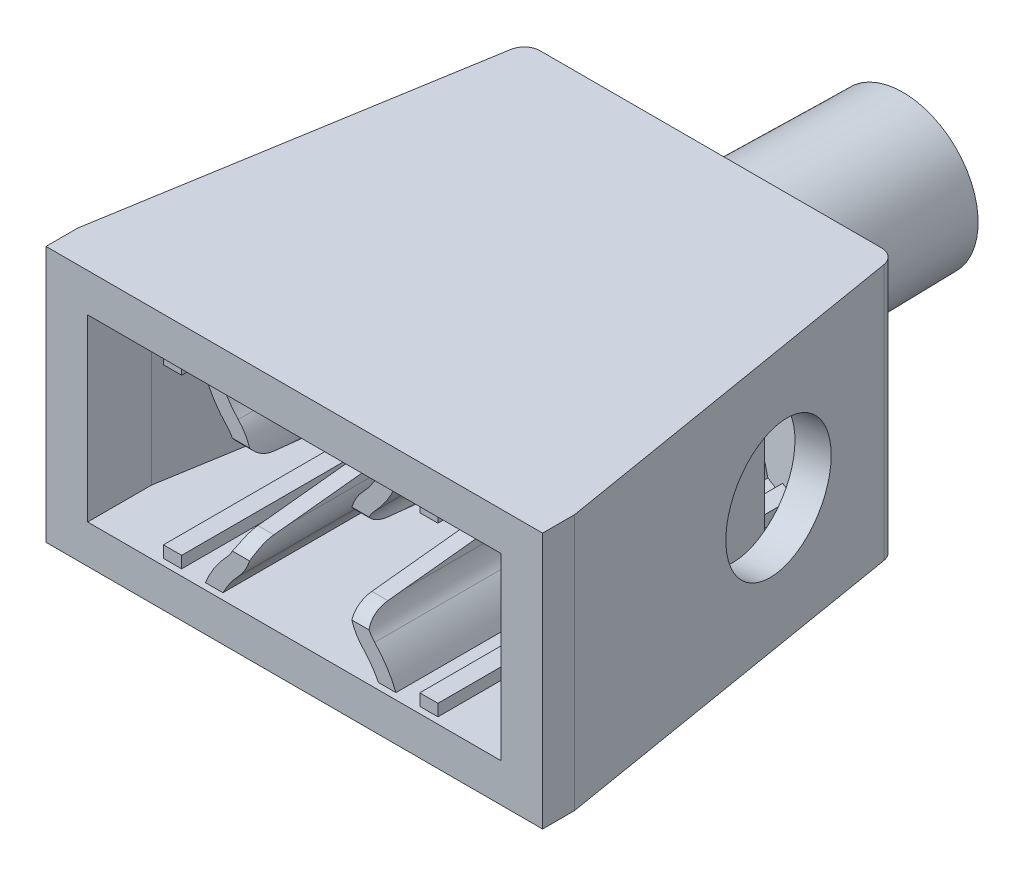
SolidWorks part; units mm, degrees
ref_plane "Front Plane" through (0, 0, 0) normal (0, 0, 1) x (1, 0, 0)
ref_plane "Top Plane" through (0, 0, 0) normal (0, 1, 0) x (1, 0, 0)
ref_plane "Right Plane" through (0, 0, 0) normal (1, 0, 0) x (0, 0, -1)
sketch "Sketch3" plane through (0, 0, 0) normal (0, 1, 0) x (1, 0, 0)
  line L0 (7.75, 0) -> (-7.75, 0)
  line L1 (-55, 0) -> (55, 0) construction
  line L2 (-7.75, 0) -> (-7.75, 1)
  line L3 (-7.75, 1) -> (-5.75, 13)
  line L4 (-5.75, 13) -> (5.75, 13)
  line L5 (0, -55) -> (0, 55) construction
  line L6 (0, 13) -> (0, 0)
  line L7 (7.75, 1) -> (5.75, 13)
  line L8 (7.75, 0) -> (7.75, 1)
  dimension "D1" = 7.75
  dimension "D2" = 1
  dimension "D3" = 5.75
  dimension "D4" = 13
extrude "Boss-Extrude1" add sketch "Sketch3" along normal blind 8 contours L4 L7 L8 L0 L2 L3
fillet "Fillet1" radius 0.5 2 edges at (5.75, 4, -13) (-5.75, 4, -13)
sketch "Sketch5" plane through (0, 0, -13) normal (0, 0, -1) x (-1, 0, 0)
  line L0 (0, 55) -> (0, -55) construction
  circle A0 centre (0, 4.196) radius 2.45
  dimension "D1" = 4.9
extrude "Boss-Extrude2" add sketch "Sketch5" along normal blind 6 draft 1
sketch "Sketch7" plane through (7.7027, 0, -1.2838) normal (0.9864, 0, -0.1644) x (-0.1644, 0, -0.9864)
  line L0 (11.4543, 0) -> (11.4543, 8) construction
  line L1 (-0.2877, 8) -> (11.4543, 8) construction
  circle A0 centre (7.4543, 4) radius 2
  dimension "D1" = 4
  dimension "D2" = 4
sketch "Sketch8" plane through (-7.7027, 0, -1.2838) normal (-0.9864, 0, -0.1644) x (-0.1644, 0, 0.9864)
  line L0 (-11.4543, 8) -> (-11.4543, 0) construction
  line L1 (0.2877, 8) -> (-11.4543, 8) construction
  circle A0 centre (-7.4543, 4) radius 2
  dimension "D1" = 4
  dimension "D2" = 4
ref_plane "Plane4" through (0, 4, 0) normal (0, 1, 0) x (1, 0, 0)
sketch "Sketch9" plane through (0, 4, 0) normal (0, 1, 0) x (1, 0, 0)
  line L0 (-6.45, 0) -> (-6.45, 2)
  line L2 (-4.4, 0) -> (4.4, 0) construction
  line L3 (-6.45, 2) -> (-4.95, 11)
  line L4 (-4.95, 11) -> (-2.4675, 12)
  line L5 (-2.4675, 12) -> (-1.4806, 12)
  line L6 (-1.4806, 12) -> (1.4806, 12)
  line L10 (6.45, 0) -> (-6.45, 0)
  line L12 (-7.75, 0) -> (-7.75, 1) construction
  line L15 (-5.3264, 13) -> (5.3264, 13) construction
  line L16 (-2.3453, 19) -> (-2.45, 13) construction
  line L17 (-7.75, 1) -> (-5.8196, 12.5822) construction
  line L19 (2.4675, 12) -> (1.4806, 12)
  line L20 (5.0967, 11) -> (2.4675, 12)
  line L21 (6.45, 2) -> (5.0967, 11)
  line L22 (6.45, 0) -> (6.45, 2)
  dimension "D1" = 2
  dimension "D2" = 1.3
  dimension "D3" = 1
  dimension "D4" = 0
  dimension "D5" = 2
  dimension "D6" = 180
  dimension "D7" = 12.9
  dimension "D8" = 2
extrude "Cut-Extrude4" cut sketch "Sketch9" against normal blind 2.8 and the other way blind 2.8
sketch "Sketch10" plane through (0, 0, -12) normal (0, 0, 1) x (1, 0, 0)
  line L0 (8.525, 4) -> (-8.525, 4) construction
  circle A0 centre (0, 4) radius 1.45
  dimension "D1" = 2.9
extrude "Cut-Extrude5" cut sketch "Sketch10" against normal blind 6 draft 1
sketch "Sketch11" plane through (0, 0, 0) normal (0, 0, 1) x (1, 0, 0)
  line L1 (2.7069, 0) -> (3.2069, 0)
  line L2 (-6.45, 6.8) -> (6.45, 6.8) construction
  line L3 (2.0286, 5.0802) -> (2.0286, 2.9198)
  line L4 (0, 8.4239) -> (0, 0)
  line L6 (8.525, 4) -> (-8.525, 4) construction
  line L7 (6.45, 6.8) -> (6.45, 1.2) construction
  line L8 (3.7177, 6.8) -> (4.2823, 6.8)
  line L9 (3.7177, 6.8) -> (3.7177, 6.4337)
  line L10 (3.7177, 6.4337) -> (4.2823, 6.4337)
  line L11 (4.2823, 6.8) -> (4.2823, 6.4337)
  line L12 (5.0967, 1.2) -> (2.4675, 1.2) construction
  line L13 (3.7166, 1.5664) -> (4.2834, 1.5664)
  line L14 (3.7166, 1.5664) -> (3.7166, 1.2)
  line L15 (3.7166, 1.2) -> (4.2834, 1.2)
  line L16 (4.2834, 1.5664) -> (4.2834, 1.2)
  line L18 (0, -4.4) -> (0, 4.4) construction
  line L19 (7.75, 8) -> (-7.75, 8) construction
  line L20 (0, 4) -> (7.7305, 4)
  line L21 (1.5286, 5.0802) -> (1.5286, 2.9198)
  line L23 (2.7069, 8) -> (3.2069, 8)
  arc A0 (2.3087, 5.7743) -> (3.2069, 8) centre (0, 8) ccw
  circle A1 centre (4, 4) radius 2.45 construction
  arc A2 (2.3087, 5.7743) -> (3.2069, 8) centre (0, 8) ccw
  arc A3 (2.3087, 5.7743) -> (2.0286, 5.0802) centre (3.0286, 5.0802) ccw
  arc A4 (2.3087, 2.2257) -> (2.0286, 2.9198) centre (3.0286, 2.9198) cw
  arc A5 (2.3087, 2.2257) -> (3.2069, 0) centre (0, 0) cw
  arc A6 (1.9487, 6.1213) -> (1.5286, 5.0802) centre (3.0286, 5.0802) ccw
  arc A7 (1.9487, 1.8787) -> (1.5286, 2.9198) centre (3.0286, 2.9198) cw
  arc A8 (1.9487, 1.8787) -> (2.7069, 0) centre (0, 0) cw
  arc A9 (1.9487, 6.1213) -> (1.5286, 5.0802) centre (3.0286, 5.0802) ccw construction
  arc A10 (1.9487, 6.1213) -> (2.7069, 8) centre (0, 8) ccw
  point P33 (2.0286, 4)
  line M6 (-6.45, 6.8) -> (6.45, 6.8)
  line M8 (6.45, 1.2) -> (-6.45, 1.2)
  dimension "D1" = 4.9
  dimension "D2" = 1
  dimension "D4" = 0.5
  dimension "D3" = 0.5
extrude "Cut-Extrude6" cut sketch "Sketch7" against normal blind 1
extrude "Cut-Extrude7" cut sketch "Sketch8" against normal blind 1
extrude "Boss-Extrude4" add sketch "Sketch11" against normal offset from surface (12.3 mm away) 12.5 from offset 0.2 contours A10 A6 L21 L20 L3 A3 A0 M6 | A7 A8 A5 A4 L3 L20 L21 M8 | L11 L9 L10 M6 | L16 L13 L14 M8 offset against normal yes
mirror "Mirror1" about plane through (0, 0, 0) normal (1, 0, 0) of "Boss-Extrude4"
sketch "Sketch12" plane through (0, 0, 0) normal (1, 0, 0) x (0, 0, -1)
  line L0 (0, 6.9104) -> (0, 6.1257)
  line L1 (0, 4.4) -> (0, -4.4) construction
  line L2 (0.8929, 5.1314) -> (3.8772, 4.8099)
  line L3 (3.8772, 3.1901) -> (0.8929, 2.8686)
  line L4 (0, 1.8743) -> (0, 1.0896)
  line L5 (0, 1.0896) -> (-0.9643, 1.0896)
  line L6 (-0.9643, 1.0896) -> (-0.9643, 6.9104)
  line L7 (-0.9643, 6.9104) -> (0, 6.9104)
  line L8 (8.525, 4) -> (-8.525, 4) construction
  arc A0 (3.8772, 4.8099) -> (3.8772, 3.1901) centre (3.7899, 4) cw
  arc A1 (0.8929, 2.8686) -> (0, 1.8743) centre (1, 1.8743) ccw
  arc A2 (0, 6.1257) -> (0.8929, 5.1314) centre (1, 6.1257) ccw
  point P16 (0, 2.7724)
  point P19 (0, 5.2276)
  dimension "D1" = 1
extrude "Cut-Extrude8" cut sketch "Sketch12" against normal blind 2.5 and the other way blind 3
